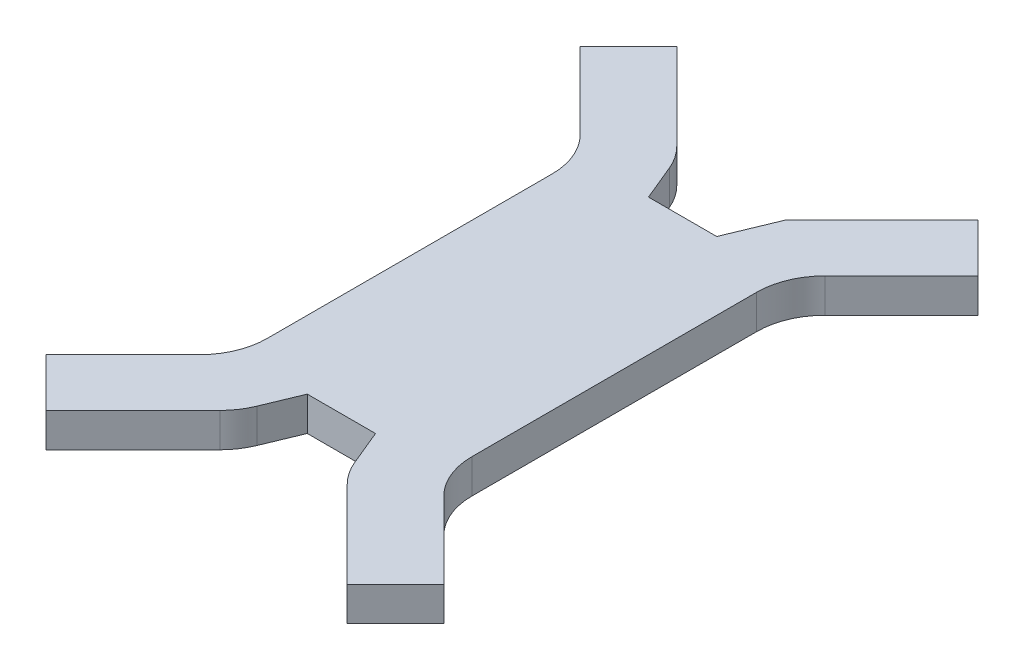
SolidWorks part; units mm, degrees
ref_plane "Front Plane" through (0, 0, 0) normal (0, 0, 1) x (1, 0, 0)
ref_plane "Top Plane" through (0, 0, 0) normal (0, 1, 0) x (1, 0, 0)
ref_plane "Right Plane" through (0, 0, 0) normal (1, 0, 0) x (0, 0, -1)
sketch "Sketch1" plane through (0, 0, 0) normal (0, 1, 0) x (1, 0, 0)
  line L0 (-65.6077, 30.5841) -> (-58.5367, 37.6551)
  line L1 (-65.6077, 30.5841) -> (-54.3945, 19.3708)
  line L2 (-58.5367, 37.6551) -> (-45.801, 24.9195)
  line L3 (-51.4656, 12.2998) -> (-51.4656, -29.4159)
  line L8 (-54.3945, -36.487) -> (-65.6077, -47.7002)
  line L9 (-65.6077, -47.7002) -> (-58.5367, -54.7713)
  line L10 (-58.5367, -54.7713) -> (-45.801, -42.0357)
  line L12 (-41.4656, -33.5581) -> (-43.6333, -38.7914)
  line L13 (-41.4656, 16.4419) -> (-43.6333, 21.6753)
  line L14 (-41.4656, 16.4419) -> (-31.4656, 16.4419)
  line L15 (-41.4656, -33.5581) -> (-31.4656, -33.5581)
  line L17 (-31.4656, 16.4419) -> (-28.5367, 23.513)
  line L18 (-31.4656, -33.5581) -> (-29.2979, -38.7914)
  line L19 (-14.3945, -54.7713) -> (-27.1301, -42.0357)
  line L20 (-7.3235, -47.7002) -> (-14.3945, -54.7713)
  line L21 (-18.5367, -36.487) -> (-7.3235, -47.7002)
  line L23 (-21.4656, 12.2998) -> (-21.4656, -29.4159)
  line L24 (-14.3945, 37.6551) -> (-28.5367, 23.513)
  line L25 (-7.3235, 30.5841) -> (-18.5367, 19.3708)
  line L26 (-7.3235, 30.5841) -> (-14.3945, 37.6551)
  arc A0 (-21.4656, 12.2998) -> (-18.5367, 19.3708) centre (-11.4656, 12.2998) cw
  arc A1 (-18.5367, -36.487) -> (-21.4656, -29.4159) centre (-11.4656, -29.4159) cw
  arc A2 (-29.2979, -38.7914) -> (-27.1301, -42.0357) centre (-20.0591, -34.9646) ccw
  arc A3 (-45.801, -42.0357) -> (-43.6333, -38.7914) centre (-52.8721, -34.9646) ccw
  arc A4 (-51.4656, -29.4159) -> (-54.3945, -36.487) centre (-61.4656, -29.4159) cw
  arc A5 (-54.3945, 19.3708) -> (-51.4656, 12.2998) centre (-61.4656, 12.2998) cw
  arc A6 (-45.801, 24.9195) -> (-43.6333, 21.6753) centre (-52.8721, 17.8484) cw
  point P30 (-51.4656, -33.5581)
  dimension "D2" = 10
  dimension "D1" = 20
extrude "Boss-Extrude1" add sketch "Sketch1" along normal blind 5
